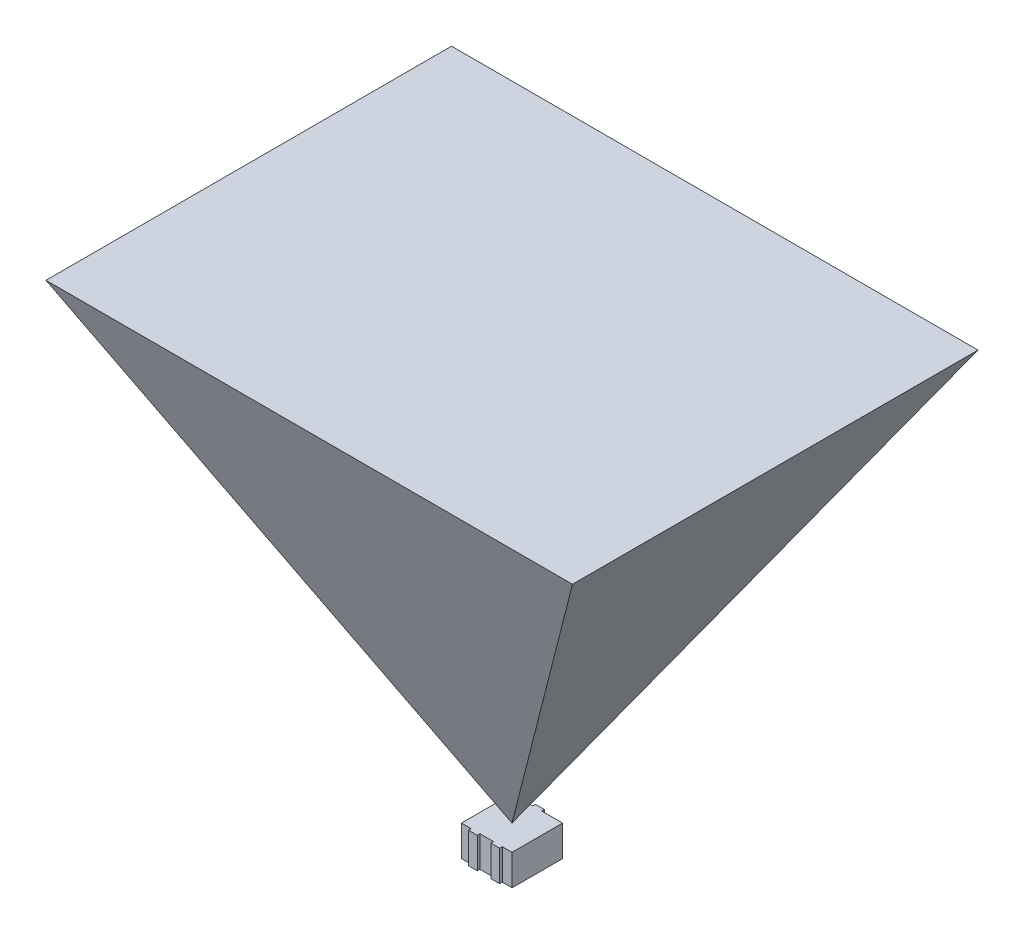
SolidWorks part; units mm, degrees
ref_plane "Ebene vorne" through (0, 0, 0) normal (0, 0, 1) x (1, 0, 0)
ref_plane "Ebene oben" through (0, 0, 0) normal (0, 1, 0) x (1, 0, 0)
ref_plane "Ebene rechts" through (0, 0, 0) normal (1, 0, 0) x (0, 0, -1)
sketch "Skizze1" plane through (0, 0, 0) normal (0, 1, 0) x (1, 0, 0)
  line L0 (-1, 5.75) -> (-1, 6.35)
  line L1 (-5.75, -5.75) -> (5.75, -5.75) construction
  line L2 (-5.75, -5.75) -> (-5.75, 5.75)
  line L3 (-5.75, -5.75) -> (-3.55, -5.75)
  line L4 (5.75, -5.75) -> (5.75, 5.75)
  line L5 (-5.75, -5.75) -> (5.75, 5.75) construction
  line L6 (-5.75, 5.75) -> (5.75, -5.75) construction
  line L7 (-1, 6.35) -> (1, 6.35)
  line L8 (1, 6.35) -> (1, 5.75)
  line L9 (1, 5.75) -> (5.75, 5.75)
  line L10 (-1, 5.75) -> (-5.75, 5.75)
  line L11 (-3.55, -5.75) -> (-3.55, -6.35)
  line L12 (-3.55, -6.35) -> (-1.55, -6.35)
  line L13 (-1.55, -6.35) -> (-1.55, -5.75)
  line L14 (-1.55, -5.75) -> (0, -5.75)
  line L15 (1.55, -5.75) -> (1.55, -6.35)
  line L16 (1.55, -6.35) -> (3.55, -6.35)
  line L17 (3.55, -6.35) -> (3.55, -5.75)
  line L18 (3.55, -5.75) -> (5.75, -5.75)
  line L19 (0, -5.75) -> (1.55, -5.75)
  point P0 (0, 0)
  dimension "D1" = 11.5
  dimension "D2" = 11.5
  dimension "D3" = 12.7
  dimension "D4" = 2
  dimension "D5" = 3.1
extrude "Aufsatz-Linear austragen1" add sketch "Skizze1" along normal blind 7
sketch "Skizze2" plane through (0, 0, 0) normal (1, 0, 0) x (0, 0, -1)
  line L0 (0, 7) -> (46.1006, 107)
  line L1 (46.1006, 107) -> (-46.1006, 107)
  line L2 (-46.1006, 107) -> (0, 7)
  line L3 (0, 7) -> (0, 107) construction
  line L4 (5.75, 7) -> (-5.75, 7) construction
  line L5 (5.75, 7) -> (-5.75, 7) construction
  dimension "D1" = 49.5
  dimension "D2" = 100
extrude "Aufsatz-Linear austragen2" add sketch "Skizze2" along normal blind 100 and the other way blind 100 separate body
sketch "Skizze3" plane through (0, 0, 0) normal (0, 0, 1) x (1, 0, 0)
  line L0 (0, 7) -> (-59.8488, 107)
  line L1 (-59.8488, 107) -> (59.8488, 107)
  line L2 (59.8488, 107) -> (0, 7)
  line L3 (0, 7) -> (0, 107) construction
  line L4 (-1.55, 7) -> (1.55, 7) construction
  line L5 (-1.55, 7) -> (1.55, 7) construction
  dimension "D1" = 100
  dimension "D2" = 61.8
extrude "Schnitt-Linear austragen1" cut sketch "Skizze3" against normal blind 100 and the other way blind 100 flip side to cut
